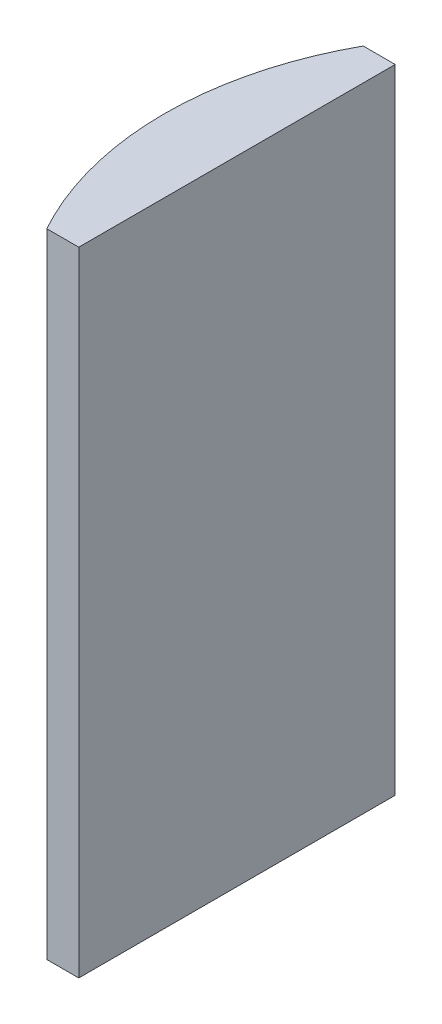
SolidWorks part; units mm, degrees
ref_plane "前视基准面" through (0, 0, 0) normal (0, 0, 1) x (1, 0, 0)
ref_plane "上视基准面" through (0, 0, 0) normal (0, 1, 0) x (1, 0, 0)
ref_plane "右视基准面" through (0, 0, 0) normal (1, 0, 0) x (0, 0, -1)
sketch "草图1" plane through (0, 0, 0) normal (0, 1, 0) x (1, 0, 0)
  line L0 (10.7432, 0) -> (-607.0701, 0) construction
  line L1 (-13.7462, 10) -> (-11.7248, 10)
  line L2 (-13.7462, -10) -> (-11.7248, -10)
  line L3 (-11.7248, 10) -> (-11.7248, -10)
  arc A0 (-13.7462, 10) -> (-13.7462, -10) centre (4.3552, 0) ccw
  point P19 (-16.3248, 0)
  point P20 (-11.7248, 0)
  dimension "D2" = 10
  dimension "D3" = 20.68
  dimension "D4" = 4.6
  dimension "D1" = 10
extrude "凸台-拉伸1" add sketch "草图1" along normal blind 40
